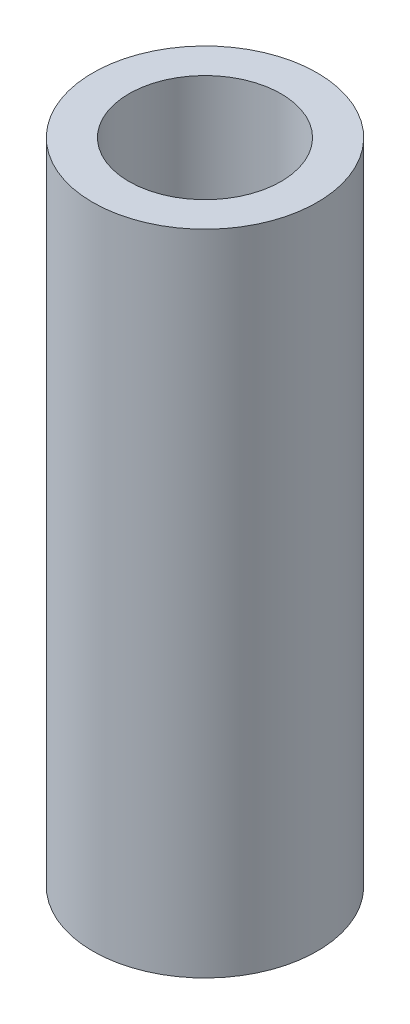
SolidWorks part; units mm, degrees
ref_plane "Front Plane" through (0, 0, 0) normal (0, 0, 1) x (1, 0, 0)
ref_plane "Top Plane" through (0, 0, 0) normal (0, 1, 0) x (1, 0, 0)
ref_plane "Right Plane" through (0, 0, 0) normal (1, 0, 0) x (0, 0, -1)
sketch "Sketch1" plane through (0, 0, 0) normal (0, 0, 1) x (1, 0, 0)
  line L0 (-3.05, -4.8017) -> (-4.5, -4.8017)
  line L4 (-4.5, -30.8017) -> (-4.5, -4.8017)
  line L5 (0, 58.5381) -> (0, -51.0237) construction
  line L6 (0, -55) -> (0, 55) construction
  line L10 (-3.05, -30.8017) -> (-3.05, -4.8017)
  line L19 (-3.05, 17.482) -> (-4.5, -4.8017) construction
  line L20 (-3.05, -17.482) -> (-4.5, -30.8017) construction
  line L21 (-3.05, -30.8017) -> (-4.5, -30.8017)
  point P0 (0, 0)
  point P6 (0, 0)
  point P11 (-5.8912, 39.9679)
  dimension "D1" = 3.05
  dimension "D2" = 4.5
  dimension "D3" = 26
revolve "Revolve1" add sketch "Sketch1" angle 360 about L5
